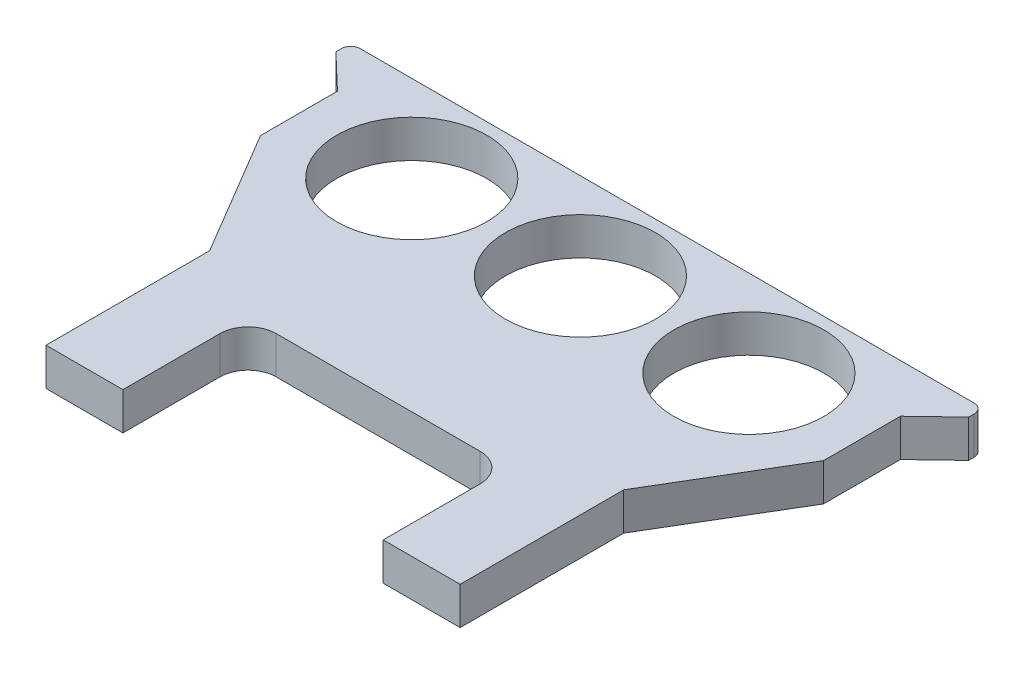
SolidWorks part; units mm, degrees
ref_plane "Piano frontale" through (0, 0, 0) normal (0, 0, 1) x (1, 0, 0)
ref_plane "Piano superiore" through (0, 0, 0) normal (0, 1, 0) x (1, 0, 0)
ref_plane "Piano destro" through (0, 0, 0) normal (1, 0, 0) x (0, 0, -1)
sketch "Schizzo2" plane through (0, 0, 0) normal (0, 1, 0) x (1, 0, 0)
  line L0 (-6.935, -4.36) -> (-6.935, 0.81)
  line L1 (-11.035, -4.36) -> (-6.935, -4.36)
  line L2 (-11.035, -4.36) -> (-11.035, 4.36)
  line L4 (11.035, -4.36) -> (11.035, 4.36)
  line L6 (16.8682, 16.9053) -> (15.01, 15.13)
  line L7 (6.935, -4.36) -> (6.935, 0.81)
  line L8 (-5.435, 2.31) -> (5.435, 2.31)
  line L9 (6.935, -4.36) -> (11.035, -4.36)
  line L13 (-14.9926, 11.0305) -> (-14.9926, 15.1305)
  line L14 (-14.9926, 11.0305) -> (-11.035, 4.36)
  line L15 (15.01, 11.03) -> (11.035, 4.36)
  line L16 (15.01, 11.03) -> (15.01, 15.13)
  line L17 (0, 2.31) -> (0, 0) construction
  line L20 (-8.985, 17.08) -> (-8.985, 17.0884) construction
  line L23 (-16.851, 16.9057) -> (-14.9926, 15.1305)
  line L24 (-14.9926, 15.1305) -> (-14.9926, 17.7005) construction
  line L25 (-14.9926, 17.7005) -> (16.3682, 17.7005)
  line L26 (-14.9926, 17.7005) -> (-16.351, 17.7005)
  line L27 (-16.851, 16.9057) -> (-16.851, 17.2005)
  line L28 (16.8682, 16.9053) -> (16.8682, 17.2005)
  arc A3 (-5.435, 2.31) -> (-6.935, 0.81) centre (-5.435, 0.81) ccw
  arc A4 (5.435, 2.31) -> (6.935, 0.81) centre (5.435, 0.81) cw
  arc A5 (-16.851, 17.2005) -> (-16.351, 17.7005) centre (-16.351, 17.2005) cw
  arc A6 (16.8682, 17.2005) -> (16.3682, 17.7005) centre (16.3682, 17.2005) ccw
  point P0 (0, 0)
  dimension "D10" = 1.5
  dimension "D11" = 1.5
  dimension "D12" = 0.5
  dimension "D15" = 0.5
  dimension "D1" = 22.07
  dimension "D2" = 8.72
  dimension "D3" = 4.1
  dimension "D4" = 4.1
  dimension "D5" = 2.57
  dimension "D6" = 4.1
  dimension "D13" = 2.57
  dimension "D14" = 2.57
extrude "Estrusione-Estrusione8" add sketch "Schizzo2" along normal blind 2 contours L25 A6 L28 L6 L16 L15 L4 L9 L7 A4 L8 A3 L0 L1 L2 L14 L13 L23 L27 A5 L26
sketch "Schizzo8" plane through (0, 0, 0) normal (0, 1, 0) x (1, 0, 0)
  circle A1 centre (-8.985, 13.0804) radius 4
  circle A2 centre (8.985, 13.0801) radius 4
  circle A3 centre (0, 13.0803) radius 4
  dimension "D1" = 8
  dimension "D2" = 8
  dimension "D3" = 8
extrude "Taglio-Estrusione6" cut sketch "Schizzo8" along normal blind 2 contours A2
sketch "Schizzo15" plane through (0, 0, 0) normal (0, 1, 0) x (1, 0, 0)
  circle A0 centre (0.0069, 13.08) radius 4
  dimension "D1" = 8
extrude "Taglio-Estrusione7" cut sketch "Schizzo15" along normal blind 2
sketch "Schizzo16" plane through (0, 0, 0) normal (0, 1, 0) x (1, 0, 0)
  circle A0 centre (-8.985, 13.0805) radius 4
  dimension "D1" = 8
extrude "Taglio-Estrusione9" cut sketch "Schizzo16" along normal blind 2
